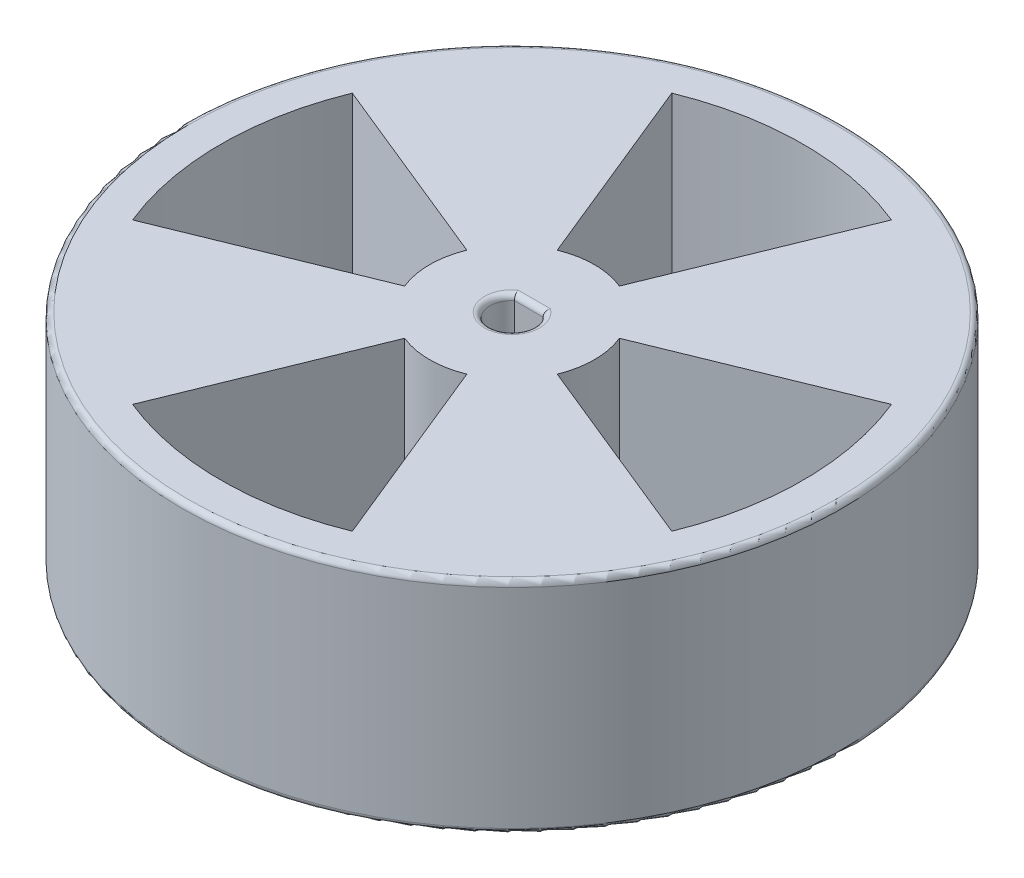
SolidWorks part; units mm, degrees
ref_plane "Front Plane" through (0, 0, 0) normal (0, 0, 1) x (1, 0, 0)
ref_plane "Top Plane" through (0, 0, 0) normal (0, 1, 0) x (1, 0, 0)
ref_plane "Right Plane" through (0, 0, 0) normal (1, 0, 0) x (0, 0, -1)
sketch "Sketch1" plane through (0, 0, 0) normal (0, 1, 0) x (1, 0, 0)
  line L0 (-1.3, 1.5199) -> (1.3, 1.5199)
  circle A0 centre (0, 0) radius 2
  circle A1 centre (0, 0) radius 30
  dimension "D1" = 4
  dimension "D3" = 60
  dimension "D2" = 2.6
extrude "Boss-Extrude1" add sketch "Sketch1" along normal blind 20 contours A1 A0 | L0 A0
fillet "Fillet1" radius 0.5 6 edges at (0, 20, 30) (0, 0, 30) (0, 0, -1.5199) (0, 20, -1.5199) (0, 0, 2) (0, 20, 2)
sketch "Sketch3" plane through (0, 20, 0) normal (0, 1, 0) x (1, 0, 0)
  line L0 (-10, 24.5408) -> (-2.8302, 6.9455)
  line L1 (2.8302, 6.9455) -> (10, 24.5408)
  line L2 (24.5408, 10) -> (6.9455, 2.8302)
  line L3 (6.9455, -2.8302) -> (24.5408, -10)
  line L4 (10, -24.5408) -> (2.8302, -6.9455)
  line L5 (-2.8302, -6.9455) -> (-10, -24.5408)
  line L6 (-24.5408, -10) -> (-6.9455, -2.8302)
  line L7 (-6.9455, 2.8302) -> (-24.5408, 10)
  circle A0 centre (0, 0) radius 7.5
  circle A4 centre (0, 0) radius 26.5
  circle A5 centre (0, 0) radius 26.5
  point P25 (0, 0)
  dimension "D1" = 15
  dimension "D3" = 20
  dimension "D2" = 3
  dimension "D4" = 4
extrude "Cut-Extrude1" cut sketch "Sketch3" against normal blind 20 contours L1 A5 L0 A0 | L7 A5 L6 A0 | L3 A5 L2 A0 | L5 A5 L4 A0
